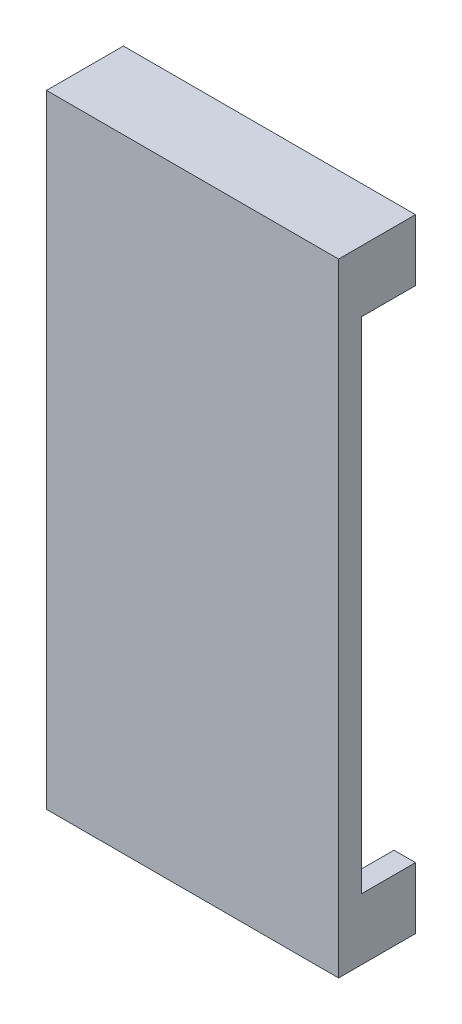
SolidWorks part; units mm, degrees
ref_plane "Front Plane" through (0, 0, 0) normal (0, 0, 1) x (1, 0, 0)
ref_plane "Top Plane" through (0, 0, 0) normal (0, 1, 0) x (1, 0, 0)
ref_plane "Right Plane" through (0, 0, 0) normal (1, 0, 0) x (0, 0, -1)
sketch "Sketch1" plane through (0, 0, 0) normal (0, 0, 1) x (1, 0, 0)
  line L0 (0, -77) -> (0, 1) construction
  line L1 (19, -78.5) -> (-19, -78.5)
  line L2 (19, -78.5) -> (19, 2.5)
  line L3 (19, 2.5) -> (-19, 2.5)
  line L4 (-19, -78.5) -> (-19, 2.5)
  line L5 (16, -77) -> (-16, -77) construction
  line L6 (19, -38) -> (-19, -38) construction
  line L7 (-16, 1) -> (16, 1) construction
  point P16 (0, -38)
  point P17 (0, -38)
  dimension "D1" = 38
  dimension "D2" = 81
extrude "Boss-Extrude1" add sketch "Sketch1" along normal blind 3
sketch "Sketch2" plane through (0, 0, 0) normal (0, 0, -1) x (-1, 0, 0)
  line L0 (-19, -5.5) -> (-19, 2.5)
  line L1 (-19, -78.5) -> (-19, 2.5) construction
  line L2 (-19, 2.5) -> (19, 2.5)
  line L3 (19, 2.5) -> (19, -5.5)
  line L4 (19, 2.5) -> (19, -78.5) construction
  line L5 (19, -5.5) -> (16.2, -5.5)
  line L6 (-19, -5.5) -> (-16.2, -5.5)
  line L7 (-16.2, -5.5) -> (-16.2, 1.2)
  line L8 (16.2, -5.5) -> (16.2, 1.2)
  line L9 (-16.2, 1.2) -> (16.2, 1.2)
  line L10 (16, 1) -> (-16, 1) construction
  line L11 (-16, -11) -> (-16, 1) construction
  line L12 (19, -38) -> (-19, -38) construction
  line L13 (-16.2, -77.2) -> (16.2, -77.2)
  line L14 (16.2, -70.5) -> (16.2, -77.2)
  line L15 (-16.2, -70.5) -> (-16.2, -77.2)
  line L16 (-19, -70.5) -> (-16.2, -70.5)
  line L17 (19, -70.5) -> (16.2, -70.5)
  line L18 (19, -78.5) -> (19, -70.5)
  line L19 (-19, -78.5) -> (19, -78.5)
  line L20 (-19, -70.5) -> (-19, -78.5)
  dimension "D1" = 0.2
  dimension "D2" = 0.2
  dimension "D3" = 8
extrude "Boss-Extrude2" add sketch "Sketch2" along normal blind 7
